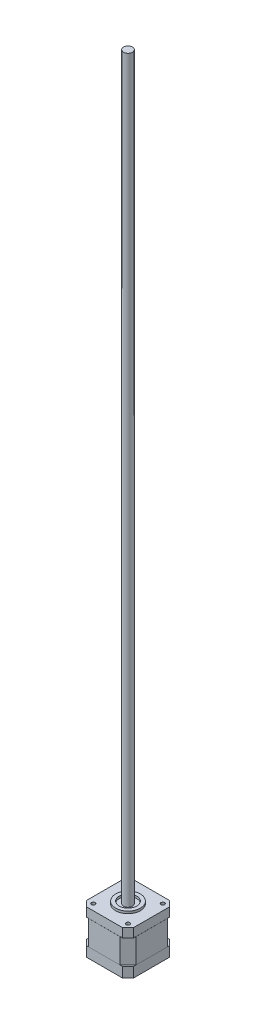
SolidWorks part; units mm, degrees
ref_plane "Plano frontal" through (0, 0, 0) normal (0, 0, 1) x (1, 0, 0)
ref_plane "Plano superior" through (0, 0, 0) normal (0, 1, 0) x (1, 0, 0)
ref_plane "Plano direito" through (0, 0, 0) normal (1, 0, 0) x (0, 0, -1)
sketch "Esboço1" plane through (0, 0, 0) normal (0, 1, 0) x (1, 0, 0)
  line L1 (21, 21) -> (-21, 21)
  line L2 (21, 21) -> (21, -21)
  line L3 (21, -21) -> (-21, -21)
  line L4 (-21, 21) -> (-21, -21)
  line L5 (21, 21) -> (-21, -21) construction
  line L6 (21, -21) -> (-21, 21) construction
  point P0 (0, 0)
  dimension "D1" = 42
  dimension "D2" = 42
extrude "Ressalto-extrusão1" add sketch "Esboço1" along normal blind 9 contours L1 L4 L3 L2
sketch "Esboço2" plane through (0, 9, 0) normal (0, 1, 0) x (1, 0, 0)
  line L0 (14, 21.05) -> (21.05, 14)
  line L1 (14, 21.05) -> (-14, 21.05)
  line L2 (21.05, 14) -> (21.05, -14)
  line L3 (14, -21.05) -> (-14, -21.05)
  line L4 (-21.05, 14) -> (-21.05, -14)
  line L5 (17.525, 17.525) -> (-17.525, -17.525) construction
  line L6 (17.525, -17.525) -> (-17.525, 17.525) construction
  line L7 (-21.05, 14) -> (-14, 21.05)
  line L8 (-21.05, -14) -> (-14, -21.05)
  line L9 (14, -21.05) -> (21.05, -14)
  point P0 (0, 0)
  dimension "D1" = 42.1
  dimension "D2" = 42.1
  dimension "D3" = 45
  dimension "D4" = 45
  dimension "D5" = 28
  dimension "D6" = 21.05
  dimension "D7" = 45
  dimension "D8" = 45
  dimension "D9" = 28
  dimension "D10" = 21.05
  dimension "D11" = 14
extrude "Ressalto-extrusão2" add sketch "Esboço2" along normal blind 22
sketch "Esboço3" plane through (0, 31, 0) normal (0, 1, 0) x (1, 0, 0)
  line L1 (21, 21) -> (-21, 21)
  line L2 (21, 21) -> (21, -21)
  line L3 (21, -21) -> (-21, -21)
  line L4 (-21, 21) -> (-21, -21)
  line L5 (21, 21) -> (-21, -21) construction
  line L6 (21, -21) -> (-21, 21) construction
  point P0 (0, 0)
extrude "Ressalto-extrusão3" add sketch "Esboço3" along normal blind 8
sketch "Esboço4" plane through (0, 39, 0) normal (0, 1, 0) x (1, 0, 0)
  circle A0 centre (0, 0) radius 11
  circle A1 centre (0, 0) radius 7.8
  dimension "D1" = 22
  dimension "D2" = 3.2
extrude "Ressalto-extrusão4" add sketch "Esboço4" along normal blind 2
hole_wizard "Broca de rosquear para tarraxa de M41" positions "Esboço6" profile "Esboço5" hole size "M4" standard "ISO"
sketch "Esboço6" plane through (0, 39, 0) normal (0, 1, 0) x (1, 0, 0)
  line L0 (-21, 21) -> (-21, -21) construction
  line L1 (21, 21) -> (-21, 21) construction
  line L2 (21.05, -14) -> (21.05, 14) construction
  line L3 (-21, -21) -> (21, -21) construction
  line L4 (21, -21) -> (21, 21) construction
  point P0 (-15.5, -15.5)
  point P2 (-15.5, 15.5)
  point P4 (15.55, 15.5)
  point P6 (15.5, -15.5)
  dimension "D1" = 5.5
  dimension "D2" = 5.5
  dimension "D3" = 5.5
  dimension "D4" = 5.5
  dimension "D5" = 5.5
sketch "Esboço5" plane through (-15.5, 39, 15.5) normal (1, 0, 0) x (0, 0, 1)
  line L0 (0, 0) -> (0, 20.9914)
  line L1 (0, 20.9914) -> (1.65, 20)
  line L2 (1.65, 20) -> (1.65, 0)
  line L5 (1.65, 0) -> (0, 0)
  line L10 (0, 20.9914) -> (-1.65, 20) construction
  line L11 (0, -6.35) -> (0, 107.95) construction
  dimension "Hole Dia." = 3.3
  dimension "Hole Depth" = 20
  dimension "Drill Angle" = 118
chamfer "Chanfro1" distance 5 angle 45 8 edges at (-21, 35, -21) (-21, 4.5, -21) (21, 4.5, -21) (21, 35, -21) (21, 4.5, 21) (21, 35, 21) (-21, 4.5, 21) (-21, 35, 21)
hole_wizard "Rebaixo para parafuso Allen sextavado de M31" positions "Esboço8" profile "Esboço9" counterbore size "M3" standard "ISO"
sketch "Esboço8" plane through (0, 0, 0) normal (0, -1, 0) x (-1, 0, 0)
  line L0 (-21, 16) -> (-21, -16) construction
  line L1 (-16, -21) -> (16, -21) construction
  line L2 (-16, 21) -> (16, 21) construction
  line L3 (21, 16) -> (21, -16) construction
  point P0 (-15.5, 15.5)
  point P2 (15.5, 15.5)
  point P4 (15.5, -15.5)
  point P6 (-15.5, -15.5)
  dimension "D1" = 5.5
  dimension "D2" = 5.5
  dimension "D3" = 5.5
  dimension "D4" = 5.5
sketch "Esboço9" plane through (15.5, 0, -15.5) normal (1, 0, 0) x (0, 0, -1)
  line L0 (0, 0) -> (0, 11.0215)
  line L1 (0, 11.0215) -> (1.7, 10)
  line L2 (1.7, 10) -> (1.7, 3.4)
  line L3 (1.7, 3.4) -> (3.25, 3.4)
  line L4 (3.25, 3.4) -> (3.25, 0)
  line L5 (3.25, 0) -> (0, 0)
  line L10 (0, 11.0215) -> (-1.7, 10) construction
  line L11 (0, -6.35) -> (0, 107.95) construction
  dimension "Hole Dia." = 3.4
  dimension "Hole Depth" = 10
  dimension "C'Bore Dia." = 6.5
  dimension "C'Bore Depth" = 3.4
  dimension "Drill Angle" = 118
sketch "Esboço10" plane through (0, 39, 0) normal (0, 1, 0) x (1, 0, 0)
  circle A0 centre (0, 0) radius 4
  dimension "D1" = 8
extrude "Boss-Extrude1" add sketch "Esboço10" along normal blind 660.4 contours A0
